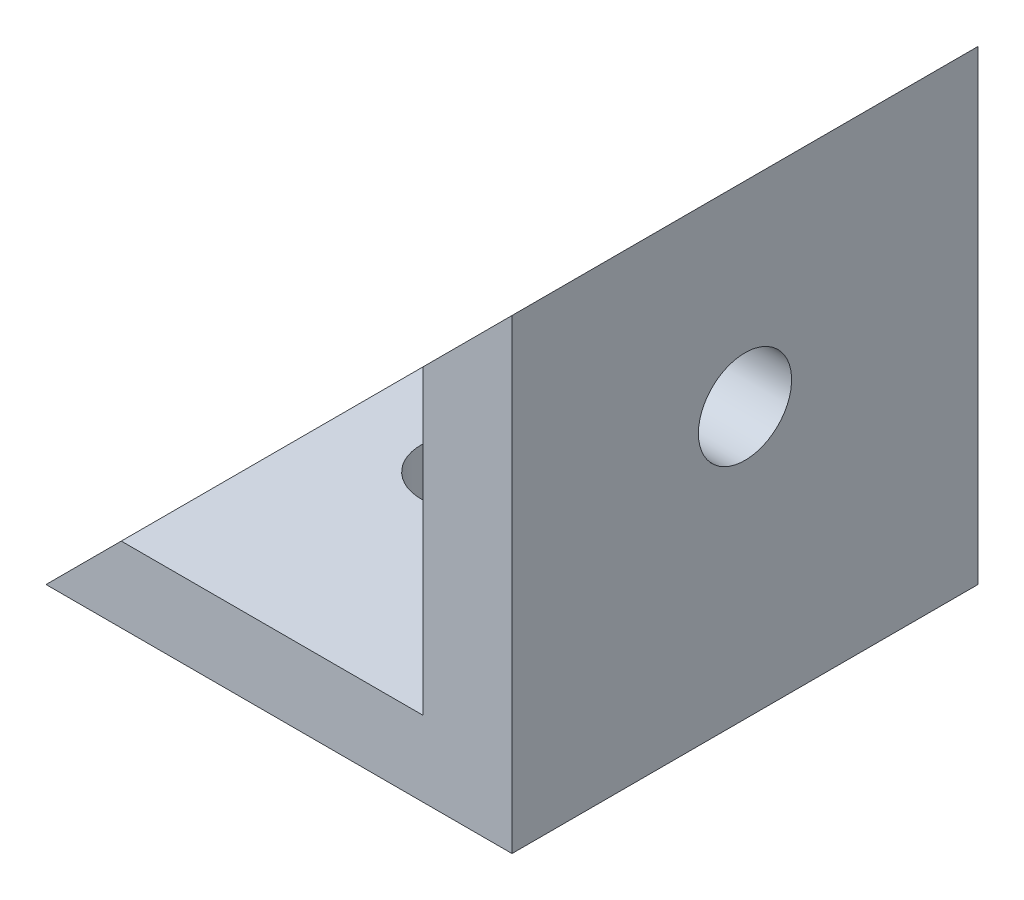
SolidWorks part; units mm, degrees
ref_plane "Front Plane" through (0, 0, 0) normal (0, 0, 1) x (1, 0, 0)
ref_plane "Top Plane" through (0, 0, 0) normal (0, 1, 0) x (1, 0, 0)
ref_plane "Right Plane" through (0, 0, 0) normal (1, 0, 0) x (0, 0, -1)
sketch "Çizim1" plane through (0, 0, 0) normal (0, 0, 1) x (1, 0, 0)
  line L1 (-23.1728, -15.6221) -> (-3.1728, -15.6221)
  line L2 (-23.1728, -15.6221) -> (-23.1728, 4.3779)
  line L3 (-23.1728, 4.3779) -> (-3.1728, 4.3779)
  line L4 (-3.1728, -15.6221) -> (-3.1728, 4.3779)
extrude "Yükseklik-Ekstrüzyon1" add sketch "Çizim1" along normal blind 20 contours L2 L1 L4 L3
sketch "Çizim2" plane through (0, 0, 20) normal (0, 0, 1) x (1, 0, 0)
  line L0 (-3.1728, 4.3779) -> (-23.1728, -15.6221)
  line L1 (-23.1728, -15.6221) -> (-23.1728, 4.3779)
  line L2 (-23.1728, 4.3779) -> (-3.1728, 4.3779)
extrude "Kes-Ekstrüzyon1" cut sketch "Çizim2" against normal blind 20
sketch "Çizim3" plane through (0, 0, 20) normal (0, 0, 1) x (1, 0, 0)
  line L2 (-6.9894, -12.392) -> (-24.214, -12.392)
  line L3 (-6.9894, -12.392) -> (-6.9894, 4.8564)
  line L4 (-6.9894, 4.8564) -> (-24.214, 4.8564)
  line L5 (-24.214, -12.392) -> (-24.214, 4.8564)
extrude "Kes-Ekstrüzyon2" cut sketch "Çizim3" against normal blind 20 contours L3 L2 L5 L4
sketch "Çizim4" plane through (-6.9894, 0, 0) normal (-1, 0, 0) x (0, 0, 1)
  line L0 (0, 4.3779) -> (20, -12.392) construction
  circle A0 centre (10, -4.007) radius 2
extrude "Kes-Ekstrüzyon3" cut sketch "Çizim4" against normal blind 20
sketch "Çizim10" plane through (0, -12.392, 0) normal (0, 1, 0) x (1, 0, 0)
  line L0 (-23.1728, 0) -> (-6.9894, -20) construction
  circle A0 centre (-15.0811, -10) radius 2
extrude "Kes-Ekstrüzyon10" cut sketch "Çizim10" against normal blind 10 contours A0
